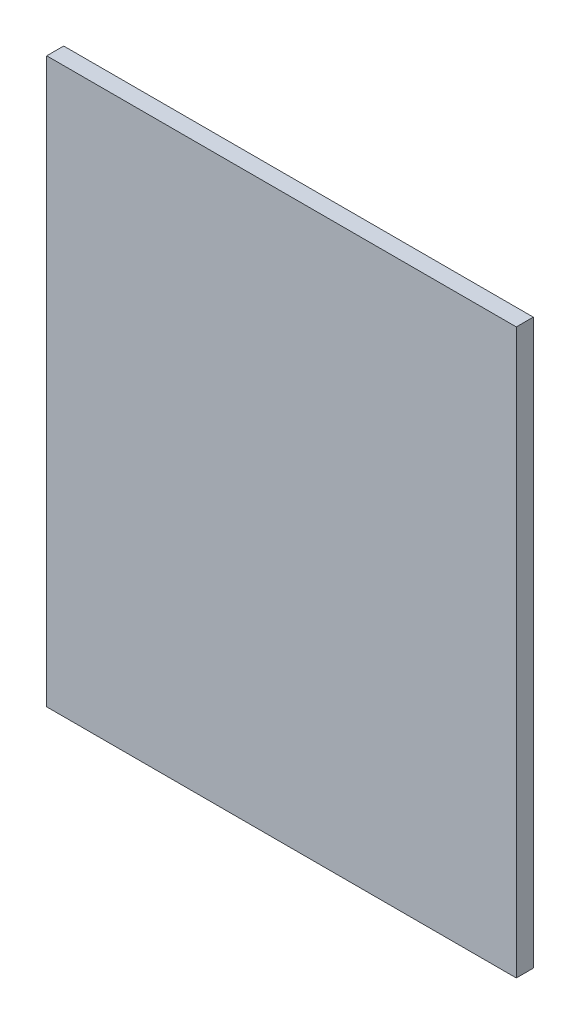
SolidWorks part; units mm, degrees
ref_plane "Front Plane" through (0, 0, 0) normal (0, 0, 1) x (1, 0, 0)
ref_plane "Top Plane" through (0, 0, 0) normal (0, 1, 0) x (1, 0, 0)
ref_plane "Right Plane" through (0, 0, 0) normal (1, 0, 0) x (0, 0, -1)
sketch "Sketch1" plane through (0, 0, 0) normal (0, 0, 1) x (1, 0, 0)
  line L1 (249, -299) -> (-249, -299)
  line L2 (249, -299) -> (249, 299)
  line L3 (249, 299) -> (-249, 299)
  line L4 (-249, -299) -> (-249, 299)
  line L5 (249, -299) -> (-249, 299) construction
  line L6 (249, 299) -> (-249, -299) construction
  point P0 (0, 0)
  dimension "D1" = 598
  dimension "D2" = 498
extrude "Boss-Extrude1" add sketch "Sketch1" along normal blind 18
equation "\"H_DSP\"=18"
equation "\"D1@Boss-Extrude1\"=\"H_DSP\""
